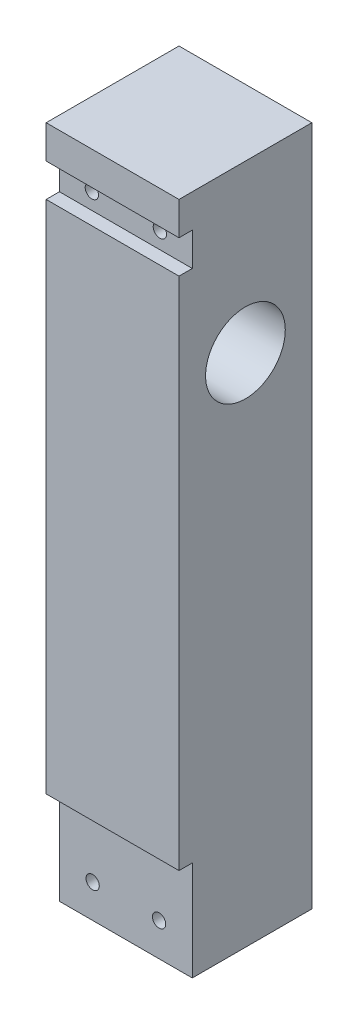
SolidWorks part; units mm, degrees
ref_plane "Front Plane" through (0, 0, 0) normal (0, 0, 1) x (1, 0, 0)
ref_plane "Top Plane" through (0, 0, 0) normal (0, 1, 0) x (1, 0, 0)
ref_plane "Right Plane" through (0, 0, 0) normal (1, 0, 0) x (0, 0, -1)
sketch "Sketch1" plane through (0, 0, 0) normal (1, 0, 0) x (0, 0, -1)
  line L0 (0, 55) -> (0, -55) construction
  line L1 (0, 120) -> (20, 120)
  line L2 (0, 120) -> (0, 0)
  line L3 (0, 0) -> (20, 0)
  line L4 (20, 120) -> (20, 0)
  line L5 (55, 0) -> (-55, 0) construction
  circle A2 centre (10, 82.5) radius 2.5
  dimension "D3" = 5
  dimension "D4" = 37.5
  dimension "D5" = 10
  dimension "D1" = 20
  dimension "D2" = 120
extrude "Boss-Extrude2" add sketch "Sketch1" against normal blind 20
ref_plane "Plane1" through (0, 0, 0) normal (1, 0, 0) x (0, 0, -1)
sketch "Sketch10" plane through (0, 0, 0) normal (1, 0, 0) x (0, 0, -1)
  circle A0 centre (10, 82.5) radius 6
  dimension "D1" = 12
extrude "Cut-Extrude1" cut sketch "Sketch10" against normal through all
ref_plane "Plane2" through (0, 0, 0) normal (0, 0, 1) x (1, 0, 0)
sketch "Sketch11" plane through (0, 0, 0) normal (0, 0, 1) x (1, 0, 0)
  line L0 (-10, 120) -> (-10, 0)
  line L1 (-20, 120) -> (0, 120) construction
  line L2 (55, 0) -> (-55, 0) construction
  line L3 (-20, 120) -> (-20, 0) construction
  line L4 (-20, 0) -> (0, 0) construction
  circle A0 centre (-15, 10) radius 1
  circle A1 centre (-5, 10) radius 1
  dimension "D1" = 2
  dimension "D2" = 5
  dimension "D3" = 10
extrude "Cut-Extrude2" cut sketch "Sketch11" against normal through all contours A0 | A1
ref_plane "Plane3" through (0, 0, -20) normal (0, 0, -1) x (-1, 0, 0)
sketch "Sketch12" plane through (0, 0, -20) normal (0, 0, -1) x (-1, 0, 0)
  circle A0 centre (5, 10) radius 2
  circle A1 centre (15, 10) radius 2
  dimension "D1" = 4
  dimension "D2" = 4
extrude "Cut-Extrude3" cut sketch "Sketch12" against normal blind 5
ref_plane "Plane4" through (0, 0, -20) normal (0, 0, -1) x (-1, 0, 0)
sketch "Sketch13" plane through (0, 0, -20) normal (0, 0, -1) x (-1, 0, 0)
  line L0 (10, 120) -> (10, 0)
  line L1 (20, 120) -> (0, 120) construction
  line L2 (55, 0) -> (-55, 0) construction
  circle A0 centre (4.8805, 100) radius 1
  circle A1 centre (15.1195, 100) radius 1
  dimension "D1" = 2
  dimension "D2" = 100
extrude "Cut-Extrude4" cut sketch "Sketch13" against normal through all contours A0 | A1
ref_plane "Plane5" through (0, 0, -20) normal (0, 0, -1) x (-1, 0, 0)
sketch "Sketch14" plane through (0, 0, -20) normal (0, 0, -1) x (-1, 0, 0)
  circle A0 centre (4.8805, 100) radius 2
  circle A1 centre (15.1195, 100) radius 2
  dimension "D1" = 4
  dimension "D2" = 4
extrude "Cut-Extrude5" cut sketch "Sketch14" against normal blind 5
ref_plane "Plane6" through (0, 0, 0) normal (0, 0, 1) x (1, 0, 0)
sketch "Sketch16" plane through (0, 0, 0) normal (0, 0, 1) x (1, 0, 0)
  line L0 (55, 0) -> (-55, 0) construction
  line L1 (-20, 102.5) -> (0, 102.5)
  line L2 (-20, 102.5) -> (-20, 97.5)
  line L3 (-20, 97.5) -> (0, 97.5)
  line L4 (0, 102.5) -> (0, 97.5)
  line L5 (-20, 102.5) -> (0, 97.5) construction
  line L6 (-20, 97.5) -> (0, 102.5) construction
  line L7 (-20, 120) -> (-20, 0) construction
  line L8 (0, -11) -> (0, 11) construction
  line L9 (-20, 20) -> (0, 20)
  line L10 (-20, 20) -> (-20, 0)
  line L11 (-20, 0) -> (0, 0)
  line L12 (0, 20) -> (0, 0)
  line L13 (-20, 20) -> (0, 0) construction
  line L14 (-20, 0) -> (0, 20) construction
  point P0 (-10, 100)
  point P9 (-10, 10)
  dimension "D1" = 100
  dimension "D2" = 10
  dimension "D3" = 5
  dimension "D4" = 20
  dimension "D5" = 10
extrude "Cut-Extrude6" cut sketch "Sketch16" against normal blind 2
ref_plane "Plane7" through (-20, 0, 0) normal (-1, 0, 0) x (0, 0, 1)
sketch "Sketch17" plane through (-20, 0, 0) normal (-1, 0, 0) x (0, 0, 1)
  line L0 (55, 0) -> (-55, 0) construction
  line L1 (-2, 0) -> (-20, 0)
  line L2 (-2, 0) -> (-2, 5)
  line L3 (-2, 5) -> (-20, 5)
  line L4 (-20, 0) -> (-20, 5)
  line L5 (-2, 20) -> (-2, 0) construction
  line L6 (-20, 11) -> (-20, -11) construction
  dimension "D1" = 5
extrude "Cut-Extrude7" cut sketch "Sketch17" against normal through all
ref_plane "Plane8" through (0, 0, 0) normal (0, 0, 1) x (1, 0, 0)
sketch "Sketch18" plane through (0, 0, 0) normal (0, 0, 1) x (1, 0, 0)
  line L0 (-20, 11) -> (-20, -11) construction
  line L1 (-20, 107.5) -> (0, 107.5)
  line L2 (-20, 107.5) -> (-20, 120)
  line L3 (-20, 120) -> (0, 120)
  line L4 (0, 107.5) -> (0, 120)
  line L5 (0, -11) -> (0, 11) construction
  line L6 (-20, 120) -> (0, 120) construction
  line L7 (0, 102.5) -> (-20, 102.5) construction
  dimension "D1" = 5
extrude "Cut-Extrude8" cut sketch "Sketch18" against normal through all
